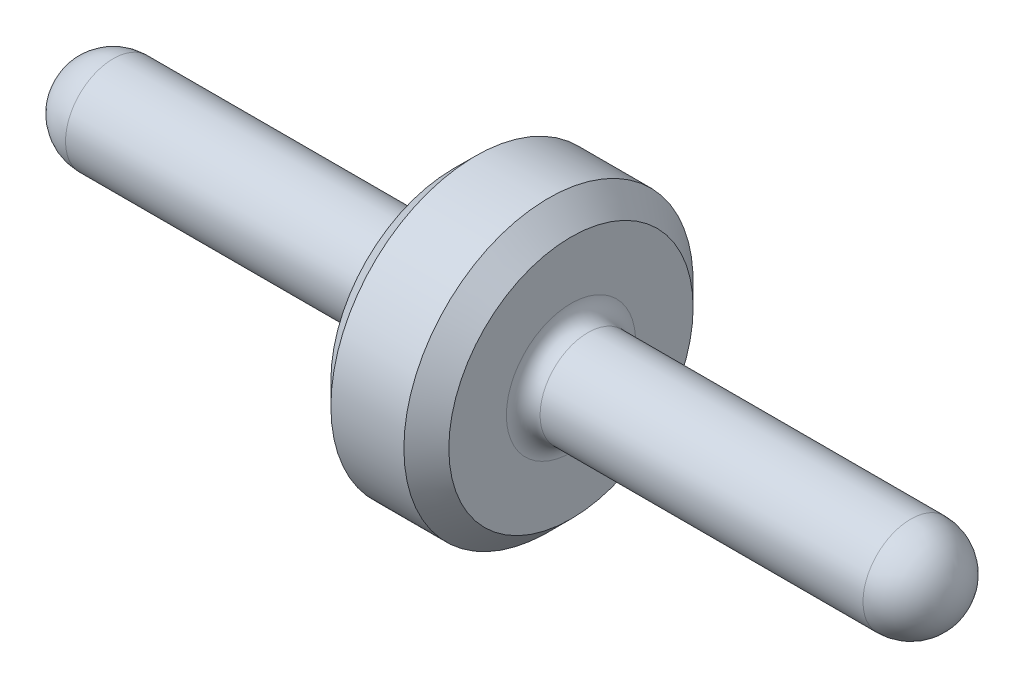
SolidWorks part; units mm, degrees
material "Brass 385"
ref_plane "Front Plane" through (0, 0, 0) normal (0, 0, 1) x (1, 0, 0)
ref_plane "Top Plane" through (0, 0, 0) normal (0, 1, 0) x (1, 0, 0)
ref_plane "Right Plane" through (0, 0, 0) normal (1, 0, 0) x (0, 0, -1)
sketch "Sketch1" plane through (0, 0, 0) normal (0, 0, 1) x (1, 0, 0)
  line L0 (0.2159, 0.2159) -> (1.6764, 0.2159)
  line L1 (0, 0) -> (4.0386, 0)
  line L2 (2.3622, 0.2159) -> (3.8227, 0.2159)
  line L3 (2.286, 0.2921) -> (2.286, 0.5525)
  line L4 (2.286, 0.5525) -> (2.1844, 0.654)
  line L5 (1.8542, 0.654) -> (2.1844, 0.654)
  line L6 (1.7526, 0.5524) -> (1.8542, 0.654)
  line L7 (1.7526, 0.2921) -> (1.7526, 0.5524)
  line L8 (0, 0) -> (4.0386, 0) construction
  arc A0 (1.6764, 0.2159) -> (1.7526, 0.2921) centre (1.6764, 0.2921) ccw
  arc A1 (0.2159, 0.2159) -> (0, 0) centre (0.2159, 0) ccw
  arc A2 (4.0386, 0) -> (3.8227, 0.2159) centre (3.8227, 0) ccw
  arc A3 (2.286, 0.2921) -> (2.3622, 0.2159) centre (2.3622, 0.2921) ccw
  dimension "D5" = 0.2159
  dimension "D9" = 0.0762
  dimension "D13" = 0.2159
  dimension "D14" = 0.0762
  dimension "D1" = 4.0386
  dimension "D2" = 1.7526
  dimension "D3" = 0.5334
  dimension "D4" = 0.2159
  dimension "D6" = 0.654
  dimension "D10" = 0.1016
  dimension "D11" = 0.1016
  dimension "D7" = 45
  dimension "D8" = 45
revolve "RevolutionAngle1" add sketch "Sketch1" angle 360 about L8
